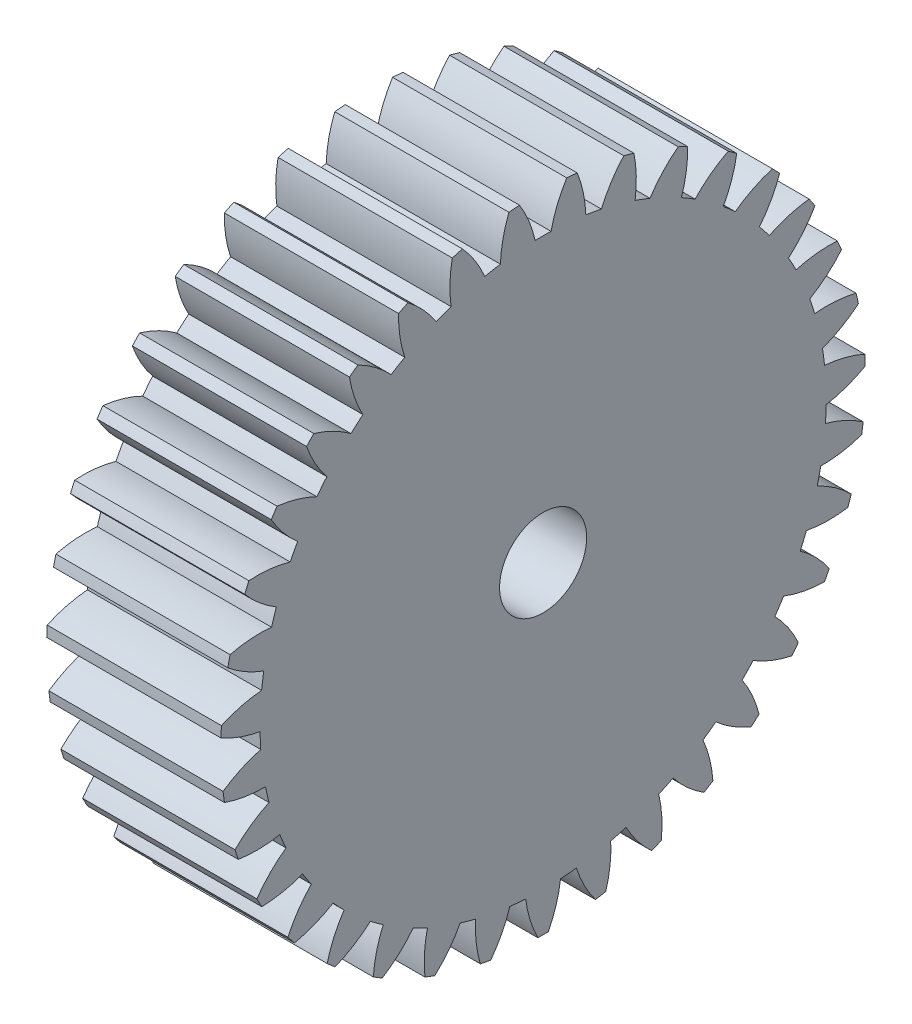
SolidWorks part; units mm, degrees
ref_plane "Plane1" through (0, 0, 0) normal (0, 0, 1) x (1, 0, 0)
ref_plane "Plane2" through (0, 0, 0) normal (0, 1, 0) x (1, 0, 0)
ref_plane "Plane3" through (0, 0, 0) normal (1, 0, 0) x (0, 0, -1)
other "Configuration Table"
sketch "HoldingSke" plane through (0, 0, 0) normal (0, 1, 0) x (1, 0, 0)
  line L0 (0, 0) -> (0.8192, -0.5736)
  line L1 (-15, 0) -> (100, 0) construction
  line L2 (0, 0) -> (-2.1039, 2.3779)
  line L3 (0, 0) -> (-11.863, 4.5341)
  line L4 (0, 0) -> (7.0742, 4.9534)
  line L5 (0, 0) -> (-46.8476, -17.4728)
  line L6 (0, 0) -> (-8.2896, -5.593)
  line L7 (-2.1039, 2.3779) -> (8.6586, 51.2059)
  line L8 (-76.2, 54.61) -> (-75.3, 54.61)
  line L9 (-71.009, 38.7566) -> (-53.1078, 45.2721)
  line L10 (-76.2, 71.12) -> (104.1128, 71.12)
  line L11 (0, 0) -> (-10, 0)
  line L12 (-76.2, 101.6) -> (-76.162, 101.6)
  line L13 (24.9733, 27.94) -> (52.9518, 28.4284)
  line L14 (24.9733, 27.94) -> (24.9743, 27.94)
  line L15 (24.9733, 27.94) -> (100.4006, 29.5858)
  line L16 (-63.627, -1) -> (-12.827, -1)
  circle A0 centre (0, 0) radius 2.5
  circle A1 centre (0, 0) radius 16.249
  circle A2 centre (0, 0) radius 37.5
  circle A3 centre (0, 0) radius 2.5
  dimension "MHD" = 32.498
  dimension "Hub_dia" = 75
  dimension "Bore" = 5
  dimension "MBD" = 5
  dimension "Num_teeth" = 35
  dimension "Pitch" = 1
  dimension "Overall_len" = 50
  dimension "Show_teeth" = 35
  dimension "Thickness" = 10
  dimension "OAL" = 50.0001
  dimension "T_dim" = 0.9
  dimension "Ap" = 20
  dimension "H" = 19.05
  dimension "Pitch_radius" = 180.3128
  dimension "Width" = 10
  dimension "Backlash" = 0.038
  dimension "Addendum_fac" = 1
  dimension "Dedendum_fac" = 1.25
  dimension "Clearance_fac" = 0.25
  dimension "Dedendum_add" = 0.001
  dimension "Module" = 1
sketch "BasProSke" plane through (0, 0, 0) normal (0, 1, 0) x (1, 0, 0)
  line L0 (-10, 0) -> (60, 0) construction
  line L1 (0, 0) -> (0, 18.5)
  line L2 (0, 0) -> (10, 0)
  line L3 (10, 0) -> (10, 18.5)
  line L4 (10, 18.5) -> (0, 18.5)
  dimension "Thickness" = 10
  dimension "Diameter" = 37
revolve "Base-Revolve" add sketch "BasProSke" angle 360 about L0
sketch "TooCutSke" plane through (0, 0, 0) normal (1, 0, 0) x (0, 0, -1)
  line L1 (0, 0) -> (0, 107) construction
  line L2 (0, 0) -> (-0.8516, 17.4793) construction
  line L3 (0, 0) -> (-3.1347, 34.8297) construction
  line L4 (-0.8516, 17.4793) -> (-1.5674, 17.4148) construction
  arc A0 (0.4564, 16.2426) -> (-0.4564, 16.2426) centre (0, 0) ccw
  arc A1 (1.373, 18.4745) -> (-1.373, 18.4745) centre (0, 0) ccw
  circle A2 centre (0, 0) radius 17.5 construction
  circle A3 centre (0, 0) radius 16.4446 construction
  arc A4 (-0.4564, 16.2426) -> (-1.373, 18.4745) centre (-7.293, 14.739) ccw
  arc A5 (1.373, 18.4745) -> (0.4564, 16.2426) centre (7.293, 14.739) ccw
  dimension "Root_dia" = 32.498
  dimension "Overcut_dia" = 37.0508
  dimension "Pitch_dia" = 35
  dimension "Base_dia" = 32.8892
  dimension "Flank_rad" = 7
  dimension "Half_ang" = 5.143
  dimension "Half_CT" = 0.7186
extrude "ToothCut" cut sketch "TooCutSke" along normal through all
fillet "Breaks" [suppressed] radius 0.02
fillet "RootFillets" [suppressed] radius 0.251
pattern_circular "TeethCuts" count 35 every 10.286 about axis through (-10, 0, 0) along (1, 0, 0) of "ToothCut", "RootFillets", "Breaks"
sketch "HubNeaOneSke" plane through (0, 0, 0) normal (-1, 0, 0) x (0, 0, 1)
  circle A0 centre (0, 0) radius 16.249
  dimension "Diameter" = 32.498
extrude "HubNearOne" [suppressed] add sketch "HubNeaOneSke" along normal blind 40.0001
sketch "HubNeaBotSke" plane through (0, 0, 0) normal (-1, 0, 0) x (0, 0, 1)
  circle A0 centre (0, 0) radius 16.249
  dimension "Diameter" = 32.498
extrude "HubNearBoth" [suppressed] add sketch "HubNeaBotSke" along normal blind 20
ref_plane "FarPln" through (10, 0, 0) normal (1, 0, 0) x (0, 0, -1)
sketch "HubFarSke" plane through (10, 0, 0) normal (1, 0, 0) x (0, 0, -1)
  circle A0 centre (0, 0) radius 16.249
  dimension "Diameter" = 32.498
extrude "HubFar" [suppressed] add sketch "HubFarSke" along normal blind 20
sketch "BorSke" plane through (0, 0, 0) normal (1, 0, 0) x (0, 0, -1)
  circle A0 centre (0, 0) radius 2.5
  dimension "Diameter" = 5
extrude "Bore" cut sketch "BorSke" along normal mid plane 100.0001
sketch "KeySke" plane through (0, 0, 0) normal (1, 0, 0) x (0, 0, -1)
  line L0 (-1, 0) -> (-1, 3.4)
  line L1 (-1, 3.4) -> (1, 3.4)
  line L2 (1, 3.4) -> (1, 0)
  line L3 (0, 0) -> (0, 34) construction
  line L4 (-1, 0) -> (1, 0)
  dimension "Offset" = 3.4
  dimension "Width" = 2
extrude "Keyway" [suppressed] cut sketch "KeySke" along normal mid plane 100.0001
pattern_circular "Keyway2" [suppressed] count 2 every 90 about axis through (-10, 0, 0) along (1, 0, 0)
equation "' \"Module@HoldingSke\" = 6.35"
equation "' \"Num_teeth@HoldingSke\" = 12"
equation "' \"Ap@HoldingSke\" =  20"
equation "' \"Ap@HoldingSke\" = 20"
equation "' \"Width@HoldingSke\" = 0.5 * 25.4"
equation "' \"Hub_dia@HoldingSke\"= 1 * 25.4"
equation "' \"Hub_dia@HoldingSke\" = 1 * 25.4"
equation "' \"Overall_len@HoldingSke\" = 1.0 * 25.4"
equation "' \"Bore@HoldingSke\" = 0.75 * 25.4"
equation "' \"T_dim@HoldingSke\" = 0.1 * 25.4"
equation "' \"Width@KeySke\" = 0.25 * 25.4"
equation "' \"Show_teeth@HoldingSke\" = 13"
equation "' \"Backlash@HoldingSke\" = 0.009 * 25.4"
equation "' \"Addendum_fac@HoldingSke\" = 1.0"
equation "' \"Dedendum_fac@HoldingSke\" = 1.25"
equation "' \"Dedendum_add@HoldingSke\" = 0.00005 * 25.4"
equation "' \"Clearance_fac@HoldingSke\" = 0.25"
equation "\"Pitch@HoldingSke\" = 1 / \"Module@HoldingSke\""
equation "\"Overcut_dia@TooCutSke\" = (\"Num_teeth@HoldingSke\" + 2 * \"Addendum_fac@HoldingSke\") / \"Pitch@HoldingSke\" + 0.002 * 25.4"
equation "\"Pitch_dia@TooCutSke\" = \"Num_teeth@HoldingSke\" / \"Pitch@HoldingSke\""
equation "\"Base_dia@TooCutSke\" = \"Num_teeth@HoldingSke\" / \"Pitch@HoldingSke\" * cos((\"Ap@HoldingSke\"  * 3.14159265 / 180))"
equation "\"Root_dia@TooCutSke\" = (\"Num_teeth@HoldingSke\" + 2) / \"Pitch@HoldingSke\" - 2 * (\"Addendum_fac@HoldingSke\" + \"Dedendum_fac@HoldingSke\") / \"Pitch@HoldingSke\" - \"Dedendum_add@HoldingSke\" * 2"
equation "\"Half_ang@TooCutSke\" = 180 / \"Num_teeth@HoldingSke\""
equation "\"Half_CT@TooCutSke\" = \"Num_teeth@HoldingSke\" / \"Pitch@HoldingSke\" * sin((3.14159265 / 2 / \"Num_teeth@HoldingSke\")) / 2 - 7 * \"Backlash@HoldingSke\" / 4"
equation "\"Flank_rad@TooCutSke\" = \"Num_teeth@HoldingSke\" / \"Pitch@HoldingSke\" / 5"
equation "\"Radius@RootFillets\" = \"Clearance_fac@HoldingSke\" / \"Pitch@HoldingSke\" + \"Dedendum_add@HoldingSke\""
equation "\"Break_rad@Breaks\" = 0.02 / \"Pitch@HoldingSke\""
equation "\"Thickness@HoldingSke\" = \"Width@HoldingSke\""
equation "\"OAL@HoldingSke\" = \"Thickness@HoldingSke\""
equation "\"MHD@HoldingSke\" = (\"Num_teeth@HoldingSke\" + 2) / \"Pitch@HoldingSke\" - 2 * (\"Addendum_fac@HoldingSke\" + \"Dedendum_fac@HoldingSke\")  / \"Pitch@HoldingSke\" - \"Dedendum_add@HoldingSke\" * 2"
equation "\"MBD@HoldingSke\" = (\"Num_teeth@HoldingSke\" + 2) / \"Pitch@HoldingSke\" - 2 * (\"Addendum_fac@HoldingSke\" + \"Dedendum_fac@HoldingSke\")  / \"Pitch@HoldingSke\" - \"Dedendum_add@HoldingSke\" * 2 - 0.002 * 25.4"
equation "\"MHD@HoldingSke\" = ((sgn( \"MHD@HoldingSke\" - \"Hub_dia@HoldingSke\" )-1)*( \"MHD@HoldingSke\" - \"Hub_dia@HoldingSke\" ))/-2+ \"Hub_dia@HoldingSke\""
equation "\"MBD@HoldingSke\" = ((sgn( \"MBD@HoldingSke\" - \"Bore@HoldingSke\" )-1)*( \"MBD@HoldingSke\" - \"Bore@HoldingSke\" ))/-2+ \"Bore@HoldingSke\""
equation "\"OAL@HoldingSke\" = ((sgn( \"OAL@HoldingSke\" - \"Overall_len@HoldingSke\" )+1)*( \"OAL@HoldingSke\" - \"Overall_len@HoldingSke\" ))/2 + \"Overall_len@HoldingSke\" + 0.000002 * 25.4"
equation "\"Num_teeth@TeethCuts\" = int( \"Show_teeth@HoldingSke\" ) + 1"
equation "\"Num_teeth@TeethCuts\" = ((sgn( \"Num_teeth@TeethCuts\" - \"Num_teeth@HoldingSke\" )-1)*( \"Num_teeth@TeethCuts\" - \"Num_teeth@HoldingSke\" ))/-2+ \"Num_teeth@HoldingSke\""
equation "\"Num_teeth@TeethCuts\" = ((sgn( \"Num_teeth@TeethCuts\" - 2.0)+1)*( \"Num_teeth@TeethCuts\" - 2.0))/2 +2.0"
equation "\"Angle@TeethCuts\" = 360.0 / \"Num_teeth@HoldingSke\""
equation "\"Diameter@BasProSke\" = (\"Num_teeth@HoldingSke\" + 2 * \"Addendum_fac@HoldingSke\") / \"Pitch@HoldingSke\""
equation "\"Thickness@BasProSke\"  = \"Thickness@HoldingSke\""
equation "' \"Fillet_rad@BasProSke\" =  \"Thickness@HoldingSke\" * 0.05"
equation "' \"Fillet_rad@BasProSke\" = \"Thickness@HoldingSke\" * 0.05"
equation "\"MHD@HoldingSke\" = ((sgn( \"MHD@HoldingSke\" - \"Root_dia@TooCutSke\" )-1)*( \"MHD@HoldingSke\" - \"Root_dia@TooCutSke\" ))/-2+ \"Root_dia@TooCutSke\""
equation "\"Diameter@HubNeaOneSke\" = \"MHD@HoldingSke\""
equation "\"Length@HubNearOne\" = \"OAL@HoldingSke\" - \"Thickness@BasProSke\""
equation "\"Diameter@HubNeaBotSke\" = \"MHD@HoldingSke\""
equation "\"Length@HubNearBoth\" = ( \"OAL@HoldingSke\" - \"Thickness@BasProSke\" ) / 2.0"
equation "\"Thickness@FarPln\" = \"Thickness@BasProSke\""
equation "\"Diameter@HubFarSke\" = \"MHD@HoldingSke\""
equation "\"Length@HubFar\" = ( \"OAL@HoldingSke\" - \"Thickness@BasProSke\" ) / 2.0"
equation "\"Diameter@BorSke\" = \"MBD@HoldingSke\""
equation "\"D1@Bore\" = \"OAL@HoldingSke\" * 2.0"
equation "\"D1@Keyway\" = \"OAL@HoldingSke\" * 2.0"
equation "\"Offset@KeySke\" = \"T_dim@HoldingSke\" + \"MBD@HoldingSke\" / 2.0"
